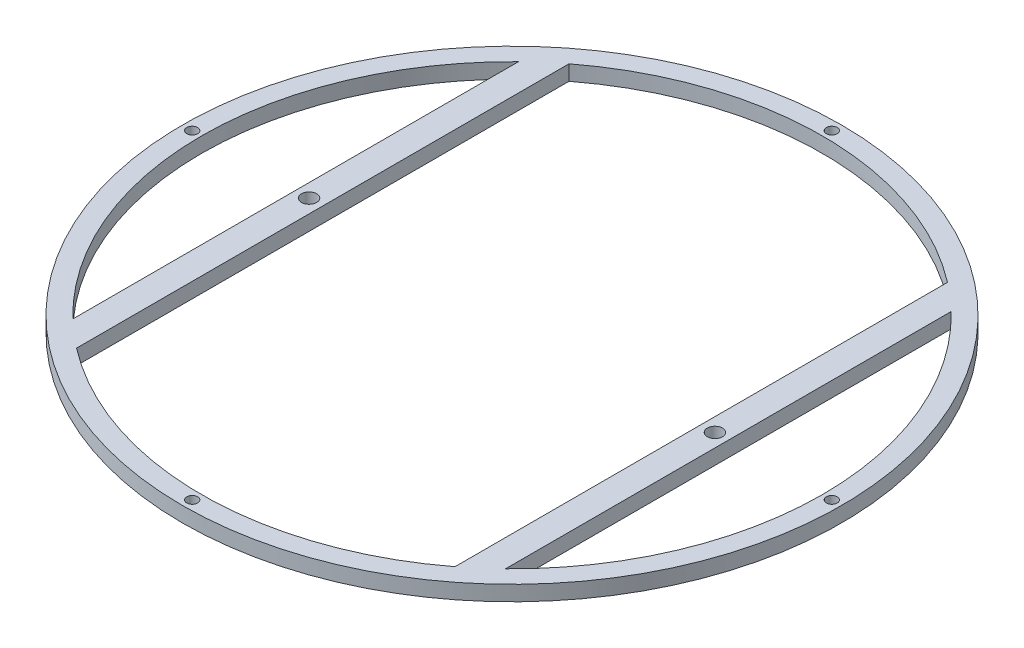
SolidWorks part; units mm, degrees
ref_plane "Front Plane" through (0, 0, 0) normal (0, 0, 1) x (1, 0, 0)
ref_plane "Top Plane" through (0, 0, 0) normal (0, 1, 0) x (1, 0, 0)
ref_plane "Right Plane" through (0, 0, 0) normal (1, 0, 0) x (0, 0, -1)
sketch "Sketch1" plane through (0, 0, 0) normal (0, 1, 0) x (1, 0, 0)
  circle A0 centre (0, 0) radius 76
  dimension "D1" = 152
extrude "Boss-Extrude1" add sketch "Sketch1" along normal blind 3.5
sketch "Sketch2" plane through (0, 3.5, 0) normal (0, 1, 0) x (1, 0, 0)
  line L0 (-49.8932, 51.3828) -> (-49.8932, -51.3828)
  line L2 (-43.6443, 56.7864) -> (-43.6443, -56.7864)
  line L4 (43.6443, 56.7864) -> (43.6443, -56.7864)
  line L5 (-43.6443, 56.7864) -> (43.6443, -56.7864) construction
  line L6 (-43.6443, -56.7864) -> (43.6443, 56.7864) construction
  line L7 (0, 71.6206) -> (0, -71.6206) construction
  line L8 (49.8932, 51.3828) -> (49.8932, -51.3828)
  arc A0 (-43.6443, -56.7864) -> (43.6443, -56.7864) centre (0, 0) ccw
  arc A1 (43.6443, 56.7864) -> (-43.6443, 56.7864) centre (0, 0) ccw
  arc A2 (-49.8932, 51.3828) -> (-49.8932, -51.3828) centre (0, 0) ccw
  arc A5 (49.8932, -51.3828) -> (49.8932, 51.3828) centre (0, 0) ccw
  point P0 (0, 0)
extrude "Cut-Extrude1" cut sketch "Sketch2" against normal through all
sketch "Sketch3" plane through (0, 3.5, 0) normal (0, 1, 0) x (1, 0, 0)
  line L0 (-49.8932, -51.3828) -> (-49.8932, 51.3828) construction
  line L1 (-43.6443, 56.7864) -> (-43.6443, -56.7864) construction
  line L2 (0, 76) -> (0, -76) construction
  line L3 (-76, 0) -> (76, 0) construction
  circle A0 centre (-46.7932, 0) radius 1.75
  circle A1 centre (0, 0) radius 76 construction
  circle A3 centre (46.7932, 0) radius 1.75
  dimension "D3" = 3.5
  dimension "D1" = 6.2489
  dimension "D2" = 3.1
extrude "Cut-Extrude2" cut sketch "Sketch3" against normal through all
sketch "Sketch5" plane through (0, 3.5, 0) normal (0, 1, 0) x (1, 0, 0)
  line L0 (0, 76) -> (0, -75) construction
  line L1 (-76, 0) -> (76, 0) construction
  circle A0 centre (0, -73.75) radius 1.25
  circle A1 centre (-73.75, 0) radius 1.25
  circle A2 centre (73.75, 0) radius 1.25
  circle A3 centre (0, 0) radius 76 construction
  circle A4 centre (0, 73.75) radius 1.25
  dimension "D1" = 73.75
  dimension "D2" = 2.5
  dimension "D3" = 73.75
  dimension "D4" = 2.5
extrude "Cut-Extrude3" cut sketch "Sketch5" against normal through all
